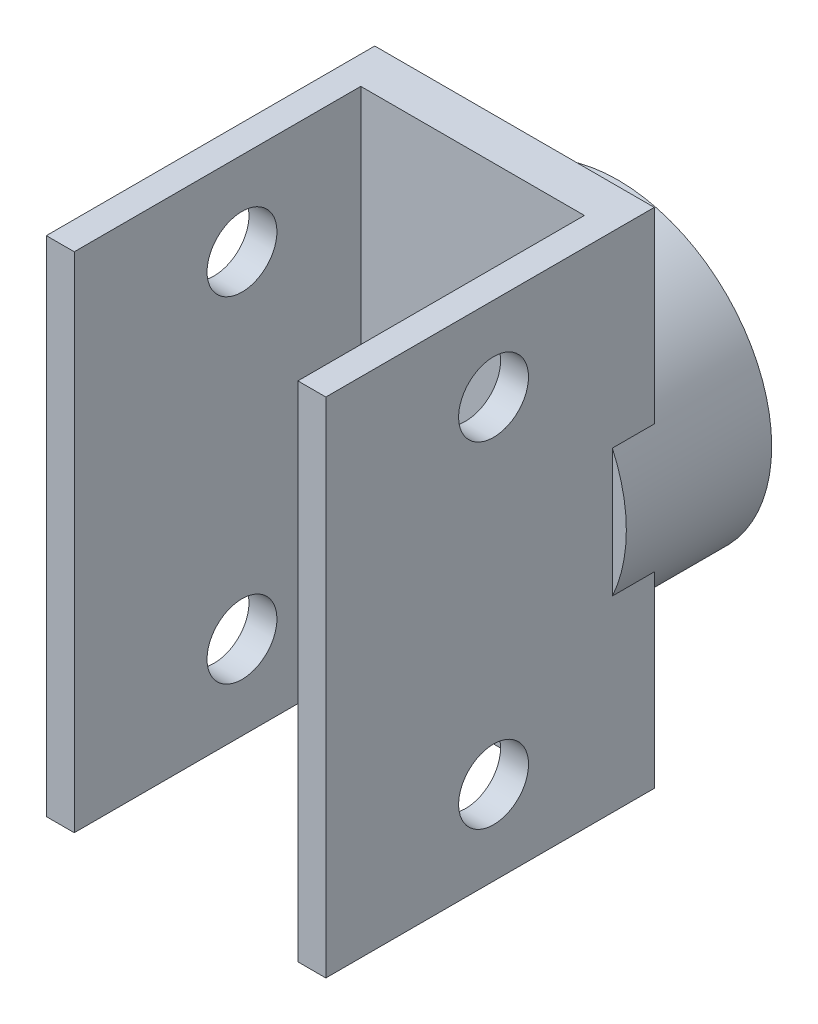
SolidWorks part; units mm, degrees
ref_plane "Front Plane" through (0, 0, 0) normal (0, 0, 1) x (1, 0, 0)
ref_plane "Top Plane" through (0, 0, 0) normal (0, 1, 0) x (1, 0, 0)
ref_plane "Right Plane" through (0, 0, 0) normal (1, 0, 0) x (0, 0, -1)
sketch "Sketch1" plane through (0, 0, 0) normal (0, 0, 1) x (1, 0, 0)
  circle A14 centre (30.5, 45) radius 11
  arc A28 (38.9837, 49.7029) -> (38.3781, 50.6591) centre (30.5, 45) ccw
  arc A29 (33.6229, 49.6484) -> (33.2987, 49.8505) centre (30.5, 45) ccw
  arc A30 (32.1126, 54.565) -> (30.9874, 54.6877) centre (30.5, 45) ccw
  arc A31 (28.8128, 50.3398) -> (28.4527, 50.2124) centre (30.5, 45) ccw
  arc A32 (24.0272, 52.2245) -> (23.2297, 51.4213) centre (30.5, 45) ccw
  arc A33 (25.2732, 47.0102) -> (25.1484, 46.6492) centre (30.5, 45) ccw
  arc A34 (20.816, 44.4438) -> (20.9467, 43.3195) centre (30.5, 45) ccw
  arc A35 (25.6695, 42.1669) -> (25.8739, 41.8442) centre (30.5, 45) ccw
  arc A36 (24.897, 37.0819) -> (25.8575, 36.4831) centre (30.5, 45) ccw
  arc A37 (29.7032, 39.457) -> (30.083, 39.4155) centre (30.5, 45) ccw
  arc A38 (33.1972, 35.6825) -> (34.2642, 36.0602) centre (30.5, 45) ccw
  arc A39 (34.3369, 40.9211) -> (34.6061, 41.1921) centre (30.5, 45) ccw
  arc A40 (39.4664, 41.2994) -> (39.8364, 42.3691) centre (30.5, 45) ccw
  arc A41 (36.0813, 45.4567) -> (36.0372, 45.8361) centre (30.5, 45) ccw
  arc A42 (38.9837, 49.7029) -> (38.3781, 50.6591) centre (30.5, 45) ccw
  arc A43 (33.6229, 49.6484) -> (33.2987, 49.8505) centre (30.5, 45) ccw
  arc A44 (32.1126, 54.565) -> (30.9874, 54.6877) centre (30.5, 45) ccw
  arc A45 (28.8128, 50.3398) -> (28.4527, 50.2124) centre (30.5, 45) ccw
  arc A46 (24.0272, 52.2245) -> (23.2297, 51.4213) centre (30.5, 45) ccw
  arc A47 (25.2732, 47.0102) -> (25.1484, 46.6492) centre (30.5, 45) ccw
  arc A48 (20.816, 44.4438) -> (20.9467, 43.3195) centre (30.5, 45) ccw
  arc A49 (25.6695, 42.1669) -> (25.8739, 41.8442) centre (30.5, 45) ccw
  arc A50 (24.897, 37.0819) -> (25.8575, 36.4831) centre (30.5, 45) ccw
  arc A51 (29.7032, 39.457) -> (30.083, 39.4155) centre (30.5, 45) ccw
  arc A52 (33.1972, 35.6825) -> (34.2642, 36.0602) centre (30.5, 45) ccw
  arc A53 (34.3369, 40.9211) -> (34.6061, 41.1921) centre (30.5, 45) ccw
  arc A54 (39.4664, 41.2994) -> (39.8364, 42.3691) centre (30.5, 45) ccw
  arc A55 (36.0813, 45.4567) -> (36.0372, 45.8361) centre (30.5, 45) ccw
  spline S56 degree 3 poles (-2125.4769, 3411.3356) (3.138, 67.6566) (30.1563, 41.5742) (37.4363, 46.9493) (37.5577, 47.0574) (37.8944, 47.3994) (38.0872, 47.6537) (38.4267, 48.2007) (38.5694, 48.488) (38.7501, 48.9354) (38.8044, 49.0865) (43.4899, 63.7718) (-13.3361, 98.0569) (3860.4658, -1130.8637) knots -6.813342 -6.813342 -6.813342 -6.813342 0.125 0.125 0.25 0.25 0.5 0.5 0.75 0.75 0.875 0.875 12.760654 12.760654 12.760654 12.760654 only from (36.8895, 46.6185) to (38.9837, 49.7029)
  spline S57 degree 3 poles (539.9034, 4018.7332) (60.7672, -17.5287) (53.0251, 48.719) (37.7441, 50.7605) (37.5845, 50.776) (37.1034, 50.8039) (36.7814, 50.7974) (36.1501, 50.7257) (35.8386, 50.6616) (35.3809, 50.5025) (35.2317, 50.4395) (27.2867, 46.1866) (30.752, 4.1996) (3197.7899, -2397.678) knots -11.765432 -11.765432 -11.765432 -11.765432 0.125 0.125 0.25 0.25 0.5 0.5 0.75 0.75 0.875 0.875 7.752629 7.752629 7.752629 7.752629 only from (38.3781, 50.6591) to (34.6945, 50.0844)
  spline S58 degree 3 poles (2996.8935, -2637.4621) (-26.8119, 131.0252) (40.9011, 56.3463) (34.4212, 49.7578) (34.3355, 49.6891) (34.1446, 49.5892) (34.0384, 49.558) (26.9801, 49.5278) (23.8401, 182.9488) (3929.5874, -846.1471) knots -21.210094 -21.210094 -21.210094 -21.210094 0.25 0.25 0.5 0.5 0.75 0.75 16.798271 16.798271 16.798271 16.798271 only from (34.6945, 50.0844) to (33.6229, 49.6484)
  spline S59 degree 3 poles (-2427.3256, 3200.3353) (157.0883, 98.9453) (36.1231, 43.8544) (33.0352, 50.1819) (33.0159, 50.2924) (33.0214, 50.507) (33.0449, 50.6138) (36.0856, 59.2915) (130.6853, 28.6452) (-3632.8593, 1650.1536) knots -15.85585 -15.85585 -15.85585 -15.85585 0.25 0.25 0.5 0.5 0.75 0.75 21.956262 21.956262 21.956262 21.956262 only from (33.2987, 49.8505) to (33.2184, 51.0047)
  spline S60 degree 3 poles (-3945.6368, 458.2654) (-4.2736, 37.7337) (32.9641, 42.5953) (33.3007, 51.6384) (33.2919, 51.8007) (33.2345, 52.2772) (33.1558, 52.5865) (32.9398, 53.1929) (32.8042, 53.4836) (32.567, 53.9039) (32.4827, 54.0405) (23.9227, 66.8599) (-38.3129, 43.8079) (3337.7718, 2306.2488) knots -6.813342 -6.813342 -6.813342 -6.813342 0.125 0.125 0.25 0.25 0.5 0.5 0.75 0.75 0.875 0.875 12.760654 12.760654 12.760654 12.760654 only from (33.2184, 51.0047) to (32.1126, 54.565)
  spline S61 degree 3 poles (-2758.6819, 2920.8497) (98.2582, 29.6778) (41.6365, 64.9296) (30.5129, 54.2553) (30.4012, 54.1402) (30.0795, 53.7814) (29.8837, 53.5256) (29.5462, 52.9873) (29.4022, 52.7038) (29.2411, 52.2468) (29.1974, 52.0909) (27.5688, 43.2276) (62.5561, 19.7584) (3915.0355, 998.3021) knots -11.765432 -11.765432 -11.765432 -11.765432 0.125 0.125 0.25 0.25 0.5 0.5 0.75 0.75 0.875 0.875 7.752629 7.752629 7.752629 7.752629 only from (30.9874, 54.6877) to (29.1401, 51.4495)
  spline S62 degree 3 poles (3977.2494, 691.732) (-72.4906, 53.8276) (28.1141, 60.2062) (29.2251, 51.0322) (29.2253, 50.9223) (29.1844, 50.7107) (29.1426, 50.6083) (24.7654, 45.071) (-81.5051, 125.8027) (3158.2681, 2537.8082) knots -21.210094 -21.210094 -21.210094 -21.210094 0.25 0.25 0.5 0.5 0.75 0.75 16.798271 16.798271 16.798271 16.798271 only from (29.1401, 51.4495) to (28.8128, 50.3398)
  spline S63 degree 3 poles (-3968.8697, 90.714) (67.2504, 177.6051) (34.9016, 48.682) (28.0294, 50.213) (27.9309, 50.2668) (27.7665, 50.4049) (27.6977, 50.4898) (22.809, 58.2777) (105.7512, 113.1309) (-3508.5268, -1818.3327) knots -15.85585 -15.85585 -15.85585 -15.85585 0.25 0.25 0.5 0.5 0.75 0.75 21.956262 21.956262 21.956262 21.956262 only from (28.4527, 50.2124) to (27.5002, 50.8691)
  spline S64 degree 3 poles (-2771.6846, -2806.0022) (14.5001, 13.2824) (33.9164, 45.4273) (27.0561, 51.3287) (26.9237, 51.4229) (26.5154, 51.6751) (26.2245, 51.8064) (25.6157, 52.0157) (25.3039, 52.0909) (24.8274, 52.1675) (24.6681, 52.1868) (9.3083, 53.4871) (-11.4722, -9.5433) (324.6348, 4040.5948) knots -6.813342 -6.813342 -6.813342 -6.813342 0.125 0.125 0.25 0.25 0.5 0.5 0.75 0.75 0.875 0.875 12.760654 12.760654 12.760654 12.760654 only from (27.5002, 50.8691) to (24.0272, 52.2245)
  spline S65 degree 3 poles (-3956.9564, -342.6073) (84.7259, 88.4223) (21.8619, 66.1328) (23.2719, 50.7806) (23.2923, 50.6216) (23.3722, 50.1464) (23.4502, 49.8338) (23.6606, 49.2343) (23.7924, 48.945) (24.0493, 48.5341) (24.144, 48.4027) (30.0582, 41.6033) (70.2214, 54.3246) (1707.1466, 3676.4263) knots -11.765432 -11.765432 -11.765432 -11.765432 0.125 0.125 0.25 0.25 0.5 0.5 0.75 0.75 0.875 0.875 7.752629 7.752629 7.752629 7.752629 only from (23.2297, 51.4213) to (24.6097, 47.958)
  spline S66 degree 3 poles (1985.6225, 3533.9238) (-40.6153, -30.0174) (17.1237, 52.6156) (24.989, 47.7642) (25.075, 47.6959) (25.2149, 47.532) (25.2689, 47.4355) (26.869, 40.5608) (-102.5082, 7.8106) (31.6756, 4044.628) knots -21.210094 -21.210094 -21.210094 -21.210094 0.25 0.25 0.5 0.5 0.75 0.75 16.798271 16.798271 16.798271 16.798271 only from (24.6097, 47.958) to (25.2732, 47.0102)
  spline S67 degree 3 poles (-2498.8069, -3053.3309) (-50.2613, 156.4105) (30.3657, 50.737) (24.8839, 46.3186) (24.7804, 46.2752) (24.57, 46.2327) (24.4607, 46.2319) (15.3239, 47.2654) (24.1515, 146.3127) (-719.2349, -3883.6915) knots -15.85585 -15.85585 -15.85585 -15.85585 0.25 0.25 0.5 0.5 0.75 0.75 21.956262 21.956262 21.956262 21.956262 only from (25.1484, 46.6492) to (24.041, 46.314)
  spline S68 degree 3 poles (512.3697, -3923.4069) (45.322, 12.7152) (32.2961, 47.9374) (23.4048, 46.2533) (23.2486, 46.2086) (22.7968, 46.0466) (22.5128, 45.901) (21.9696, 45.5556) (21.7164, 45.3586) (21.3594, 45.0339) (21.245, 44.9213) (10.6517, 33.7233) (46.9745, -21.8224) (-2909.9918, 2766.1764) knots -6.813342 -6.813342 -6.813342 -6.813342 0.125 0.125 0.25 0.25 0.5 0.5 0.75 0.75 0.875 0.875 12.760654 12.760654 12.760654 12.760654 only from (24.041, 46.314) to (20.816, 44.4438)
  spline S69 degree 3 poles (-2152.5948, -3314.1881) (30.3604, 114.4689) (8.5919, 51.4225) (21.4739, 42.953) (21.611, 42.8698) (22.0323, 42.636) (22.3253, 42.5021) (22.9252, 42.2928) (23.2336, 42.2155) (23.715, 42.1601) (23.8768, 42.1522) (32.8802, 42.5367) (47.9756, 81.8692) (-1763.2913, 3620.0124) knots -11.765432 -11.765432 -11.765432 -11.765432 0.125 0.125 0.25 0.25 0.5 0.5 0.75 0.75 0.875 0.875 7.752629 7.752629 7.752629 7.752629 only from (20.9467, 43.3195) to (24.5148, 42.2391)
  spline S70 degree 3 poles (-1581.6437, 3705.3449) (47.1483, -55.4497) (16.2409, 39.3099) (24.9043, 42.4152) (25.0111, 42.4396) (25.2262, 42.4465) (25.3362, 42.4281) (31.7988, 39.3296) (-26.0564, -84.9997) (-3121.3835, 2507.1403) knots -20.990345 -20.990345 -20.990345 -20.990345 0.25 0.25 0.5 0.5 0.75 0.75 17.120907 17.120907 17.120907 17.120907 only from (24.5148, 42.2391) to (25.6695, 42.1669)
  spline S71 degree 3 poles (875.8756, -3864.2695) (-106.9581, 51.3216) (25.9309, 48.4719) (25.9675, 41.4313) (25.9369, 41.3233) (25.8389, 41.1323) (25.7714, 41.0463) (19.2666, 34.5473) (-52.6677, 103.2039) (2634.6226, -2990.6655) knots -15.85585 -15.85585 -15.85585 -15.85585 0.25 0.25 0.5 0.5 0.75 0.75 21.956262 21.956262 21.956262 21.956262 only from (25.8739, 41.8442) to (25.4455, 40.7694)
  spline S72 degree 3 poles (3433.5663, -2052.5203) (64.9827, 36.459) (29.3232, 48.2357) (25.0963, 40.2342) (25.0339, 40.0841) (24.8789, 39.6299) (24.8156, 39.3171) (24.747, 38.6771) (24.7431, 38.3563) (24.7744, 37.8747) (24.7911, 37.7151) (26.9413, 22.4511) (93.0155, 16.2172) (-3930.3681, -557.3433) knots -6.813342 -6.813342 -6.813342 -6.813342 0.125 0.125 0.25 0.25 0.5 0.5 0.75 0.75 0.875 0.875 12.760654 12.760654 12.760654 12.760654 only from (25.4455, 40.7694) to (24.897, 37.0819)
  spline S73 degree 3 poles (1295.6817, -3756.2318) (-23.9, 88.204) (11.8192, 31.876) (26.4727, 36.6669) (26.6232, 36.7221) (27.0687, 36.9057) (27.3561, 37.0513) (27.8938, 37.3898) (28.1465, 37.5828) (28.4899, 37.9246) (28.5969, 38.0462) (33.9099, 45.3251) (12.5704, 81.6506) (-3882.9678, 871.5412) knots -11.765432 -11.765432 -11.765432 -11.765432 0.125 0.125 0.25 0.25 0.5 0.5 0.75 0.75 0.875 0.875 7.752629 7.752629 7.752629 7.752629 only from (25.8575, 36.4831) to (28.9269, 38.5992)
  spline S74 degree 3 poles (-3806.0048, 1174.7449) (119.4612, -7.6393) (26.0519, 30.2645) (29.0314, 39.012) (29.0789, 39.1111) (29.2075, 39.284) (29.2896, 39.3581) (35.6359, 42.4479) (96.3541, -76.3979) (-3869.1106, -843.8549) knots -21.210094 -21.210094 -21.210094 -21.210094 0.25 0.25 0.5 0.5 0.75 0.75 16.798271 16.798271 16.798271 16.798271 only from (28.9269, 38.5992) to (29.7032, 39.457)
  spline S75 degree 3 poles (3613.973, -1731.4484) (-60.1461, -58.5277) (24.9367, 43.5924) (30.4641, 39.2313) (30.5295, 39.1401) (30.6177, 38.9444) (30.6428, 38.8379) (31.6684, 29.7002) (-66.8599, 16.2664) (4027.5227, 188.2786) knots -15.85585 -15.85585 -15.85585 -15.85585 0.25 0.25 0.5 0.5 0.75 0.75 21.956262 21.956262 21.956262 21.956262 only from (30.083, 39.4155) to (30.6562, 38.4105)
  spline S76 degree 3 poles (3792.1846, 1397.8419) (58.6772, 66.6344) (27.2365, 46.0974) (30.8569, 37.8038) (30.9353, 37.6614) (31.1938, 37.257) (31.3989, 37.0125) (31.8566, 36.5599) (32.1049, 36.3568) (32.5009, 36.081) (32.6361, 35.9945) (45.9106, 28.1586) (91.9811, 75.9308) (-1968.1299, -3427.2862) knots -6.813342 -6.813342 -6.813342 -6.813342 0.125 0.125 0.25 0.25 0.5 0.5 0.75 0.75 0.875 0.875 12.760654 12.760654 12.760654 12.760654 only from (30.6562, 38.4105) to (33.1972, 35.6825)
  spline S77 degree 3 poles (3791.2505, -1335.8704) (-37.1961, 29.4056) (29.1135, 22.2121) (34.5041, 36.6557) (34.5548, 36.8079) (34.689, 37.2706) (34.7544, 37.5861) (34.8249, 38.2175) (34.8317, 38.5354) (34.7785, 39.0171) (34.7502, 39.1765) (32.3719, 47.8687) (-9.3335, 53.8333) (-3055.7232, -2499.3323) knots -11.765432 -11.765432 -11.765432 -11.765432 0.125 0.125 0.25 0.25 0.5 0.5 0.75 0.75 0.875 0.875 7.752629 7.752629 7.752629 7.752629 only from (34.2642, 36.0602) to (34.5235, 39.7792)
  spline S78 degree 3 poles (-3244.7918, -2250.1158) (127.1215, 81.7326) (39.2473, 32.3349) (34.2659, 40.1184) (34.2181, 40.2172) (34.1631, 40.4256) (34.1563, 40.536) (35.6975, 47.4241) (166.4721, 20.7964) (-1705.9327, -3558.0303) knots -21.210094 -21.210094 -21.210094 -21.210094 0.25 0.25 0.5 0.5 0.75 0.75 16.798271 16.798271 16.798271 16.798271 only from (34.5235, 39.7792) to (34.3369, 40.9211)
  spline S79 degree 3 poles (3653.6421, 1739.0746) (54.9242, -90.4184) (28.1318, 39.7728) (34.9878, 41.3752) (35.0999, 41.3695) (35.3079, 41.3164) (35.4067, 41.2697) (43.1903, 36.3742) (-7.7381, -49.0341) (2410.5832, 3259.331) knots -15.85585 -15.85585 -15.85585 -15.85585 0.25 0.25 0.5 0.5 0.75 0.75 21.956262 21.956262 21.956262 21.956262 only from (34.6061, 41.1921) to (35.7492, 41.0136)
  spline S80 degree 3 poles (1318.1776, 3829.4865) (31.1537, 80.5186) (27.6073, 43.1327) (36.3488, 40.7923) (36.5089, 40.7648) (36.9863, 40.7148) (37.3053, 40.7227) (37.9446, 40.7983) (38.2582, 40.8658) (38.7207, 41.0035) (38.8726, 41.0553) (53.2755, 46.5481) (44.6501, 112.3529) (1499.1173, -3682.5268) knots -6.813342 -6.813342 -6.813342 -6.813342 0.125 0.125 0.25 0.25 0.5 0.5 0.75 0.75 0.875 0.875 12.760654 12.760654 12.760654 12.760654 only from (35.7492, 41.0136) to (39.4664, 41.2994)
  spline S81 degree 3 poles (3454.8976, 2124.3146) (0.4844, -17.6499) (47.4519, 29.7079) (39.5204, 42.928) (39.433, 43.0624) (39.1548, 43.4559) (38.949, 43.7037) (38.4993, 44.1525) (38.255, 44.356) (37.8452, 44.6148) (37.7029, 44.692) (29.4243, 48.2521) (-1.2419, 19.3644) (95.5104, -3954.2717) knots -11.765432 -11.765432 -11.765432 -11.765432 0.125 0.125 0.25 0.25 0.5 0.5 0.75 0.75 0.875 0.875 7.752629 7.752629 7.752629 7.752629 only from (39.8364, 42.3691) to (37.0904, 44.8906)
  spline S82 degree 3 poles (-217.2172, -3946.7076) (62.0238, 143.4441) (45.8559, 43.9424) (36.6646, 44.9007) (36.5575, 44.9249) (36.3603, 45.0119) (36.2698, 45.0754) (31.8453, 50.575) (134.2003, 136.2166) (1764.8144, -3559.0504) knots -21.210094 -21.210094 -21.210094 -21.210094 0.25 0.25 0.5 0.5 0.75 0.75 16.798271 16.798271 16.798271 16.798271 only from (37.0904, 44.8906) to (36.0813, 45.4567)
  spline S83 degree 3 poles (965.0113, 3933.9248) (151.6027, -20.3364) (33.1102, 39.8894) (36.132, 46.2487) (36.2065, 46.3327) (36.3776, 46.4623) (36.4758, 46.5104) (45.1562, 49.5436) (80.1778, -43.5251) (-998.6075, 3909.9265) knots -15.85585 -15.85585 -15.85585 -15.85585 0.25 0.25 0.5 0.5 0.75 0.75 21.956262 21.956262 21.956262 21.956262 only from (36.0372, 45.8361) to (36.8895, 46.6185)
  spline S84 degree 3 poles (36.8895, 46.6185) (37.0434, 46.6741) (37.1787, 46.759) (37.4363, 46.9493) (37.5577, 47.0574) (37.8944, 47.3994) (38.0872, 47.6537) (38.4267, 48.2007) (38.5694, 48.488) (38.7501, 48.9354) (38.8044, 49.0865) (38.9019, 49.3922) (38.9439, 49.5472) (38.9837, 49.7029) knots 0 0 0 0 0.125 0.125 0.25 0.25 0.5 0.5 0.75 0.75 0.875 0.875 1 1 1 1
  spline S85 degree 3 poles (38.3781, 50.6591) (38.2202, 50.6897) (38.062, 50.718) (37.7441, 50.7605) (37.5845, 50.776) (37.1034, 50.8039) (36.7814, 50.7974) (36.1501, 50.7257) (35.8386, 50.6616) (35.3809, 50.5025) (35.2317, 50.4395) (34.9481, 50.2876) (34.81, 50.1992) (34.6945, 50.0844) knots 0 0 0 0 0.125 0.125 0.25 0.25 0.5 0.5 0.75 0.75 0.875 0.875 1 1 1 1
  spline S86 degree 3 poles (34.6945, 50.0844) (34.635, 49.9946) (34.5705, 49.9095) (34.4212, 49.7578) (34.3355, 49.6891) (34.1446, 49.5892) (34.0384, 49.558) (33.8219, 49.5571) (33.7145, 49.589) (33.6229, 49.6484) knots 0 0 0 0 0.25 0.25 0.5 0.5 0.75 0.75 1 1 1 1
  spline S87 degree 3 poles (33.2987, 49.8505) (33.2052, 49.9065) (33.1296, 49.9884) (33.0352, 50.1819) (33.0159, 50.2924) (33.0214, 50.507) (33.0449, 50.6138) (33.1158, 50.816) (33.1639, 50.9117) (33.2184, 51.0047) knots 0 0 0 0 0.25 0.25 0.5 0.5 0.75 0.75 1 1 1 1
  spline S88 degree 3 poles (33.2184, 51.0047) (33.2709, 51.1596) (33.2888, 51.3183) (33.3007, 51.6384) (33.2919, 51.8007) (33.2345, 52.2772) (33.1558, 52.5865) (32.9398, 53.1929) (32.8042, 53.4836) (32.567, 53.9039) (32.4827, 54.0405) (32.3046, 54.3073) (32.2095, 54.4368) (32.1126, 54.565) knots 0 0 0 0 0.125 0.125 0.25 0.25 0.5 0.5 0.75 0.75 0.875 0.875 1 1 1 1
  spline S89 degree 3 poles (30.9874, 54.6877) (30.8651, 54.5834) (30.7443, 54.4774) (30.5129, 54.2553) (30.4012, 54.1402) (30.0795, 53.7814) (29.8837, 53.5256) (29.5462, 52.9873) (29.4022, 52.7038) (29.2411, 52.2468) (29.1974, 52.0909) (29.1393, 51.7744) (29.1223, 51.6114) (29.1401, 51.4495) knots 0 0 0 0 0.125 0.125 0.25 0.25 0.5 0.5 0.75 0.75 0.875 0.875 1 1 1 1
  spline S90 degree 3 poles (29.1401, 51.4495) (29.1732, 51.347) (29.1995, 51.2435) (29.2251, 51.0322) (29.2253, 50.9223) (29.1844, 50.7107) (29.1426, 50.6083) (29.0083, 50.4384) (28.9164, 50.3744) (28.8128, 50.3398) knots 0 0 0 0 0.25 0.25 0.5 0.5 0.75 0.75 1 1 1 1
  spline S91 degree 3 poles (28.4527, 50.2124) (28.3506, 50.1742) (28.2394, 50.1662) (28.0294, 50.213) (27.9309, 50.2668) (27.7665, 50.4049) (27.6977, 50.4898) (27.5838, 50.6713) (27.539, 50.7686) (27.5002, 50.8691) knots 0 0 0 0 0.25 0.25 0.5 0.5 0.75 0.75 1 1 1 1
  spline S92 degree 3 poles (27.5002, 50.8691) (27.4118, 51.0068) (27.2989, 51.1198) (27.0561, 51.3287) (26.9237, 51.4229) (26.5154, 51.6751) (26.2245, 51.8064) (25.6157, 52.0157) (25.3039, 52.0909) (24.8274, 52.1675) (24.6681, 52.1868) (24.3484, 52.2139) (24.1879, 52.2203) (24.0272, 52.2245) knots 0 0 0 0 0.125 0.125 0.25 0.25 0.5 0.5 0.75 0.75 0.875 0.875 1 1 1 1
  spline S93 degree 3 poles (23.2297, 51.4213) (23.235, 51.2606) (23.2426, 51.1001) (23.2719, 50.7806) (23.2923, 50.6216) (23.3722, 50.1464) (23.4502, 49.8338) (23.6606, 49.2343) (23.7924, 48.945) (24.0493, 48.5341) (24.144, 48.4027) (24.3551, 48.16) (24.4721, 48.045) (24.6097, 47.958) knots 0 0 0 0 0.125 0.125 0.25 0.25 0.5 0.5 0.75 0.75 0.875 0.875 1 1 1 1
  spline S94 degree 3 poles (24.6097, 47.958) (24.7105, 47.92) (24.8078, 47.876) (24.989, 47.7642) (25.075, 47.6959) (25.2149, 47.532) (25.2689, 47.4355) (25.318, 47.2245) (25.3108, 47.1128) (25.2732, 47.0102) knots 0 0 0 0 0.25 0.25 0.5 0.5 0.75 0.75 1 1 1 1
  spline S95 degree 3 poles (25.1484, 46.6492) (25.1146, 46.5456) (25.0515, 46.4537) (24.8839, 46.3186) (24.7804, 46.2752) (24.57, 46.2327) (24.4607, 46.2319) (24.2477, 46.256) (24.1438, 46.2817) (24.041, 46.314) knots 0 0 0 0 0.25 0.25 0.5 0.5 0.75 0.75 1 1 1 1
  spline S96 degree 3 poles (24.041, 46.314) (23.8782, 46.3308) (23.7195, 46.3129) (23.4048, 46.2533) (23.2486, 46.2086) (22.7968, 46.0466) (22.5128, 45.901) (21.9696, 45.5556) (21.7164, 45.3586) (21.3594, 45.0339) (21.245, 44.9213) (21.0245, 44.6882) (20.9194, 44.5668) (20.816, 44.4438) knots 0 0 0 0 0.125 0.125 0.25 0.25 0.5 0.5 0.75 0.75 0.875 0.875 1 1 1 1
  spline S97 degree 3 poles (20.9467, 43.3195) (21.0757, 43.2234) (21.2059, 43.1293) (21.4739, 42.953) (21.611, 42.8698) (22.0323, 42.636) (22.3253, 42.5021) (22.9252, 42.2928) (23.2336, 42.2155) (23.715, 42.1601) (23.8768, 42.1522) (24.1982, 42.166) (24.361, 42.1857) (24.5148, 42.2391) knots 0 0 0 0 0.125 0.125 0.25 0.25 0.5 0.5 0.75 0.75 0.875 0.875 1 1 1 1
  spline S98 degree 3 poles (24.5148, 42.2391) (24.6074, 42.2942) (24.7027, 42.343) (24.9043, 42.4152) (25.0111, 42.4396) (25.2262, 42.4465) (25.3362, 42.4281) (25.5306, 42.3349) (25.6129, 42.26) (25.6695, 42.1669) knots 0 0 0 0 0.25 0.25 0.5 0.5 0.75 0.75 1 1 1 1
  spline S99 degree 3 poles (25.8739, 41.8442) (25.9338, 41.7532) (25.9664, 41.6465) (25.9675, 41.4313) (25.9369, 41.3233) (25.8389, 41.1323) (25.7714, 41.0463) (25.6198, 40.8949) (25.5349, 40.8296) (25.4455, 40.7694) knots 0 0 0 0 0.25 0.25 0.5 0.5 0.75 0.75 1 1 1 1
  spline S100 degree 3 poles (25.4455, 40.7694) (25.331, 40.6526) (25.2459, 40.5174) (25.0963, 40.2342) (25.0339, 40.0841) (24.8789, 39.6299) (24.8156, 39.3171) (24.747, 38.6771) (24.7431, 38.3563) (24.7744, 37.8747) (24.7911, 37.7151) (24.8358, 37.3973) (24.8653, 37.2395) (24.897, 37.0819) knots 0 0 0 0 0.125 0.125 0.25 0.25 0.5 0.5 0.75 0.75 0.875 0.875 1 1 1 1
  spline S101 degree 3 poles (25.8575, 36.4831) (26.013, 36.5241) (26.1678, 36.5672) (26.4727, 36.6669) (26.6232, 36.7221) (27.0687, 36.9057) (27.3561, 37.0513) (27.8938, 37.3898) (28.1465, 37.5828) (28.4899, 37.9246) (28.5969, 38.0462) (28.7866, 38.306) (28.8727, 38.4456) (28.9269, 38.5992) knots 0 0 0 0 0.125 0.125 0.25 0.25 0.5 0.5 0.75 0.75 0.875 0.875 1 1 1 1
  spline S102 degree 3 poles (28.9269, 38.5992) (28.9415, 38.7059) (28.9628, 38.8106) (29.0314, 39.012) (29.0789, 39.1111) (29.2075, 39.284) (29.2896, 39.3581) (29.4843, 39.4529) (29.5949, 39.4707) (29.7032, 39.457) knots 0 0 0 0 0.25 0.25 0.5 0.5 0.75 0.75 1 1 1 1
  spline S103 degree 3 poles (30.083, 39.4155) (30.1915, 39.4056) (30.2952, 39.3646) (30.4641, 39.2313) (30.5295, 39.1401) (30.6177, 38.9444) (30.6428, 38.8379) (30.6667, 38.625) (30.6649, 38.5179) (30.6562, 38.4105) knots 0 0 0 0 0.25 0.25 0.5 0.5 0.75 0.75 1 1 1 1
  spline S104 degree 3 poles (30.6562, 38.4105) (30.6761, 38.2481) (30.7288, 38.0973) (30.8569, 37.8038) (30.9353, 37.6614) (31.1938, 37.257) (31.3989, 37.0125) (31.8566, 36.5599) (32.1049, 36.3568) (32.5009, 36.081) (32.6361, 35.9945) (32.9125, 35.8314) (33.0542, 35.756) (33.1972, 35.6825) knots 0 0 0 0 0.125 0.125 0.25 0.25 0.5 0.5 0.75 0.75 0.875 0.875 1 1 1 1
  spline S105 degree 3 poles (34.2642, 36.0602) (34.3291, 36.2073) (34.392, 36.3552) (34.5041, 36.6557) (34.5548, 36.8079) (34.689, 37.2706) (34.7544, 37.5861) (34.8249, 38.2175) (34.8317, 38.5354) (34.7785, 39.0171) (34.7502, 39.1765) (34.6653, 39.4868) (34.6098, 39.6411) (34.5235, 39.7792) knots 0 0 0 0 0.125 0.125 0.25 0.25 0.5 0.5 0.75 0.75 0.875 0.875 1 1 1 1
  spline S106 degree 3 poles (34.5235, 39.7792) (34.4493, 39.8572) (34.3806, 39.9391) (34.2659, 40.1184) (34.2181, 40.2172) (34.1631, 40.4256) (34.1563, 40.536) (34.2036, 40.7474) (34.2586, 40.8449) (34.3369, 40.9211) knots 0 0 0 0 0.25 0.25 0.5 0.5 0.75 0.75 1 1 1 1
  spline S107 degree 3 poles (34.6061, 41.1921) (34.6815, 41.2708) (34.7782, 41.3263) (34.9878, 41.3752) (35.0999, 41.3695) (35.3079, 41.3164) (35.4067, 41.2697) (35.5881, 41.1556) (35.6707, 41.0874) (35.7492, 41.0136) knots 0 0 0 0 0.25 0.25 0.5 0.5 0.75 0.75 1 1 1 1
  spline S108 degree 3 poles (35.7492, 41.0136) (35.8886, 40.9279) (36.0394, 40.8751) (36.3488, 40.7923) (36.5089, 40.7648) (36.9863, 40.7148) (37.3053, 40.7227) (37.9446, 40.7983) (38.2582, 40.8658) (38.7207, 41.0035) (38.8726, 41.0553) (39.1724, 41.1696) (39.3198, 41.2335) (39.4664, 41.2994) knots 0 0 0 0 0.125 0.125 0.25 0.25 0.5 0.5 0.75 0.75 0.875 0.875 1 1 1 1
  spline S109 degree 3 poles (39.8364, 42.3691) (39.7619, 42.5116) (39.6854, 42.6529) (39.5204, 42.928) (39.433, 43.0624) (39.1548, 43.4559) (38.949, 43.7037) (38.4993, 44.1525) (38.255, 44.356) (37.8452, 44.6148) (37.7029, 44.692) (37.4074, 44.8191) (37.2522, 44.872) (37.0904, 44.8906) knots 0 0 0 0 0.125 0.125 0.25 0.25 0.5 0.5 0.75 0.75 0.875 0.875 1 1 1 1
  spline S110 degree 3 poles (37.0904, 44.8906) (36.9831, 44.8812) (36.8763, 44.8786) (36.6646, 44.9007) (36.5575, 44.9249) (36.3603, 45.0119) (36.2698, 45.0754) (36.134, 45.2441) (36.092, 45.348) (36.0813, 45.4567) knots 0 0 0 0 0.25 0.25 0.5 0.5 0.75 0.75 1 1 1 1
  spline S111 degree 3 poles (36.0372, 45.8361) (36.0227, 45.9441) (36.0397, 46.0543) (36.132, 46.2487) (36.2065, 46.3327) (36.3776, 46.4623) (36.4758, 46.5104) (36.6781, 46.5811) (36.7829, 46.6031) (36.8895, 46.6185) knots 0 0 0 0 0.25 0.25 0.5 0.5 0.75 0.75 1 1 1 1
  dimension "D2" = 22
  dimension "D1" = 0.2
extrude "Boss-Extrude1" add sketch "Sketch1" along normal up to surface (7.4 mm away)
sketch "Sketch3" plane through (0, 0, 7.4) normal (0, 0, 1) x (1, 0, 0)
  circle A0 centre (30.5, 45) radius 11 construction
  circle A1 centre (30.5, 45) radius 11
extrude "Boss-Extrude2" add sketch "Sketch3" along normal blind 3
sketch "Sketch4" plane through (0, 0, 10.4) normal (0, 0, 1) x (1, 0, 0)
  line L1 (20.5, 63) -> (40.5, 63)
  line L2 (20.5, 63) -> (20.5, 27)
  line L3 (20.5, 27) -> (40.5, 27)
  line L4 (40.5, 63) -> (40.5, 27)
  line L5 (20.5, 63) -> (40.5, 27) construction
  line L6 (20.5, 27) -> (40.5, 63) construction
  point P0 (30.5, 45)
  dimension "D1" = 20
  dimension "D2" = 36
extrude "Boss-Extrude3" add sketch "Sketch4" against normal blind 3
sketch "Sketch5" plane through (0, 0, 10.4) normal (0, 0, 1) x (1, 0, 0)
  line L0 (20.5, 27) -> (40.5, 27) construction
  line L1 (20.5, 63) -> (22.5, 63)
  line L2 (20.5, 63) -> (20.5, 27)
  line L3 (20.5, 27) -> (22.5, 27)
  line L4 (22.5, 63) -> (22.5, 27)
  line L6 (40.5, 63) -> (38.5, 63)
  line L7 (40.5, 63) -> (40.5, 27)
  line L8 (40.5, 27) -> (38.5, 27)
  line L9 (38.5, 63) -> (38.5, 27)
  dimension "D1" = 2
  dimension "D2" = 2
extrude "Boss-Extrude4" add sketch "Sketch5" along normal blind 20.5
sketch "Sketch6" plane through (40.5, 0, 0) normal (1, 0, 0) x (0, 0, -1)
  line L0 (-7.4, 27) -> (-30.9, 27) construction
  line L2 (-30.9, 27) -> (-30.9, 63) construction
  line L3 (-7.4, 63) -> (-30.9, 63) construction
  circle A0 centre (-18.9, 33) radius 2.5
  circle A1 centre (-18.9, 57) radius 2.5
  dimension "D1" = 5
  dimension "D2" = 5
  dimension "D3" = 6
  dimension "12" = 12
  dimension "D5" = 6
extrude "Cut-Extrude1" cut sketch "Sketch6" against normal through all
